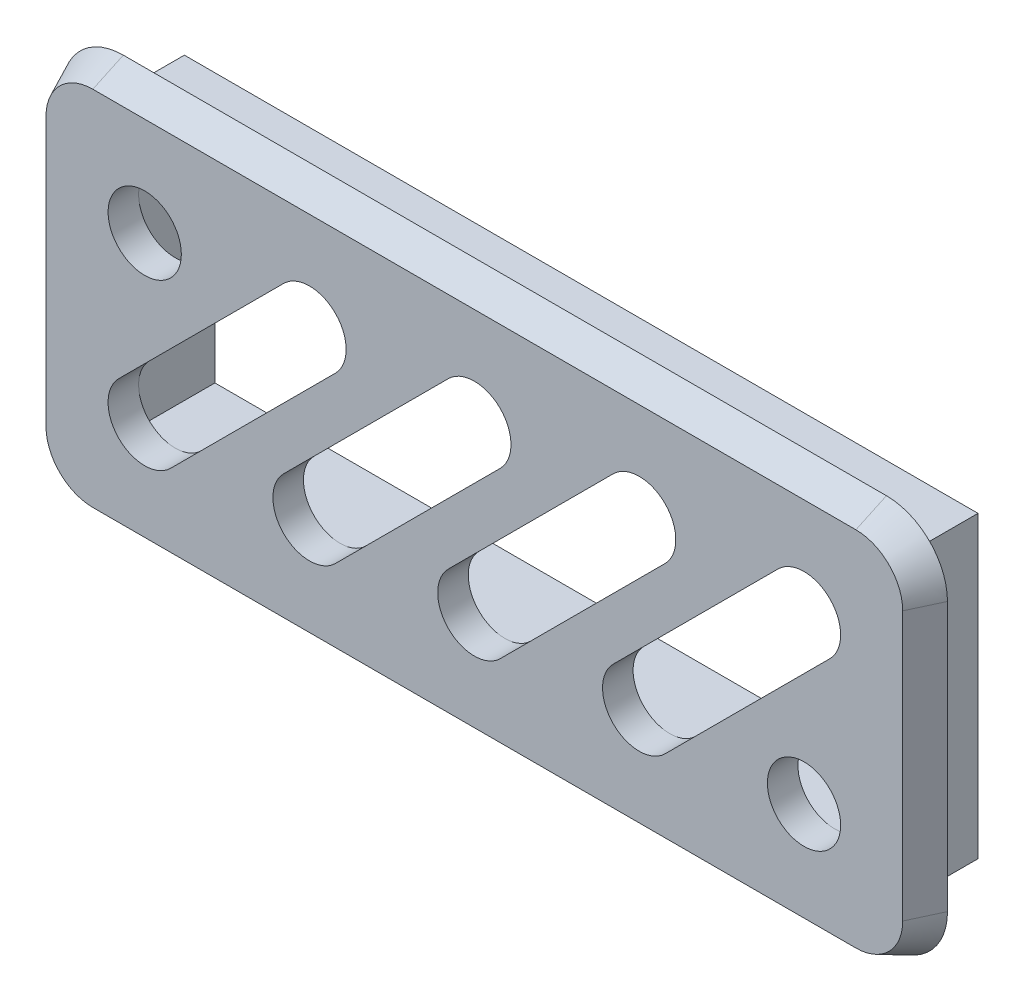
SolidWorks part; units mm, degrees
ref_plane "前视基准面" through (0, 0, 0) normal (0, 0, 1) x (1, 0, 0)
ref_plane "上视基准面" through (0, 0, 0) normal (0, 1, 0) x (1, 0, 0)
ref_plane "右视基准面" through (0, 0, 0) normal (1, 0, 0) x (0, 0, -1)
other "Configuration Table"
sketch "草图1" plane through (0, 0, 0) normal (0, 0, 1) x (1, 0, 0)
  line L4 (32.6638, -12.1008) -> (32.6638, -4.3008)
  line L5 (32.6638, -4.3008) -> (8.6638, -4.3008)
  line L6 (8.6638, -4.3008) -> (8.6638, -12.1008)
  line L7 (8.6638, -12.1008) -> (32.6638, -12.1008)
  line L8 (33.6638, -13.1008) -> (33.6638, -3.3008)
  line L9 (7.6638, -13.1008) -> (33.6638, -13.1008)
  line L10 (7.6638, -3.3008) -> (7.6638, -13.1008)
  line L11 (33.6638, -3.3008) -> (7.6638, -3.3008)
  line L12 (33.6638, -13.1008) -> (33.6638, -3.3008)
  line L13 (7.6638, -13.1008) -> (33.6638, -13.1008)
  line L14 (7.6638, -3.3008) -> (7.6638, -13.1008)
  line L15 (33.6638, -3.3008) -> (7.6638, -3.3008)
  dimension "D1" = 0.1
extrude "凸台-拉伸1" add sketch "草图1" against normal blind 2.5
sketch "草图2" plane through (0, 0, 0) normal (0, 0, 1) x (1, 0, 0)
  line L8 (35.1638, -14.6008) -> (35.1638, -1.8008)
  line L9 (6.1638, -14.6008) -> (35.1638, -14.6008)
  line L10 (6.1638, -1.8008) -> (6.1638, -14.6008)
  line L11 (35.1638, -1.8008) -> (6.1638, -1.8008)
  line L12 (35.1638, -12.6008) -> (35.1638, -3.8008)
  line L13 (8.1638, -14.6008) -> (33.1638, -14.6008)
  line L14 (6.1638, -3.8008) -> (6.1638, -12.6008)
  line L15 (33.1638, -1.8008) -> (8.1638, -1.8008)
  arc A0 (35.1638, -3.8008) -> (33.1638, -1.8008) centre (33.1638, -3.8008) ccw
  arc A1 (35.1638, -12.6008) -> (33.1638, -14.6008) centre (33.1638, -12.6008) cw
  arc A2 (8.1638, -14.6008) -> (6.1638, -12.6008) centre (8.1638, -12.6008) cw
  arc A3 (6.1638, -3.8008) -> (8.1638, -1.8008) centre (8.1638, -3.8008) cw
  dimension "D2" = 2
  dimension "D1" = 1.5
extrude "凸台-拉伸2" add sketch "草图2" along normal blind 1 draft 25
sketch "草图3" plane through (0, 0, 0) normal (0, 0, -1) x (-1, 0, 0)
  line L0 (-31.4638, -5.5008) -> (-26.0638, -10.9008) construction
  line L1 (-30.6153, -4.6523) -> (-25.2153, -10.0523)
  line L2 (-45.8827, -5.5008) -> (-41.0684, -5.5008) construction
  line L6 (-32.3124, -6.3493) -> (-26.9124, -11.7493)
  line L7 (-26.0638, -5.5008) -> (-20.6638, -10.9008) construction
  line L10 (-50.9645, -10.9008) -> (-43.5902, -10.9008) construction
  line L13 (-25.2153, -4.6523) -> (-19.8153, -10.0523)
  line L16 (-26.9124, -6.3493) -> (-21.5124, -11.7493)
  line L19 (-32.6638, -12.1008) -> (-32.6638, -4.3008) construction
  line L22 (-20.6638, -5.5008) -> (-15.2638, -10.9008) construction
  line L25 (-8.6638, -12.1008) -> (-32.6638, -12.1008) construction
  line L26 (-19.8153, -4.6523) -> (-14.4153, -10.0523)
  line L27 (-21.5124, -6.3493) -> (-16.1124, -11.7493)
  line L28 (-15.2638, -5.5008) -> (-9.8638, -10.9008) construction
  line L29 (-14.4153, -4.6523) -> (-9.0153, -10.0523)
  line L30 (-16.1124, -6.3493) -> (-10.7124, -11.7493)
  line L32 (-32.6638, -4.3008) -> (-8.6638, -4.3008) construction
  circle A74 centre (-31.4638, -10.9008) radius 1.2
  arc A75 (-30.6153, -4.6523) -> (-32.3124, -6.3493) centre (-31.4638, -5.5008) ccw
  arc A76 (-26.9124, -11.7493) -> (-25.2153, -10.0523) centre (-26.0638, -10.9008) ccw
  arc A77 (-25.2153, -4.6523) -> (-26.9124, -6.3493) centre (-26.0638, -5.5008) ccw
  arc A78 (-21.5124, -11.7493) -> (-19.8153, -10.0523) centre (-20.6638, -10.9008) ccw
  arc A79 (-19.8153, -4.6523) -> (-21.5124, -6.3493) centre (-20.6638, -5.5008) ccw
  arc A80 (-16.1124, -11.7493) -> (-14.4153, -10.0523) centre (-15.2638, -10.9008) ccw
  arc A81 (-14.4153, -4.6523) -> (-16.1124, -6.3493) centre (-15.2638, -5.5008) ccw
  arc A82 (-10.7124, -11.7493) -> (-9.0153, -10.0523) centre (-9.8638, -10.9008) ccw
  circle A83 centre (-9.8638, -5.5008) radius 1.2
  point P15 (-28.7638, -8.2008)
  point P23 (-23.3638, -8.2008)
  point P30 (-17.9638, -8.2008)
  point P37 (-12.5638, -8.2008)
  dimension "D3" = 5.4
  dimension "D2" = 1.2
  dimension "D1" = 1.2
  dimension "D4" = 4
extrude "切除-拉伸1" cut sketch "草图3" against normal up to next
